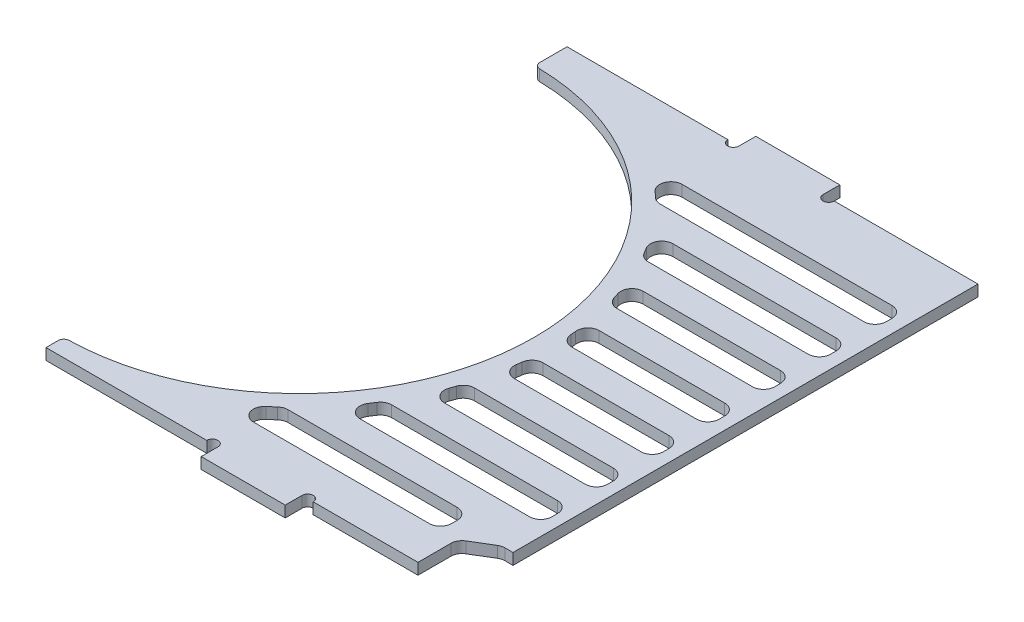
SolidWorks part; units mm, degrees
ref_plane "前视基准面" through (0, 0, 0) normal (0, 0, 1) x (1, 0, 0)
ref_plane "上视基准面" through (0, 0, 0) normal (0, 1, 0) x (1, 0, 0)
ref_plane "右视基准面" through (0, 0, 0) normal (1, 0, 0) x (0, 0, -1)
sketch "草图1" plane through (0, 0, 0) normal (0, 1, 0) x (1, 0, 0)
  line L0 (-38.2, -44.69) -> (-38.2, -45.85)
  line L1 (-38.2, 45.85) -> (38.2, 45.85)
  line L2 (-38.2, 45.85) -> (-38.2, 39.31)
  line L3 (-38.2, -45.85) -> (38.2, -45.85)
  line L4 (38.2, 45.85) -> (38.2, -45.85)
  line L5 (-38.2, 45.85) -> (38.2, -45.85) construction
  line L6 (-38.2, -45.85) -> (38.2, 45.85) construction
  arc A0 (-38.2, -44.69) -> (-38.2, 39.31) centre (-38.2, -2.69) ccw
  point P0 (0, 0)
  dimension "D4" = 84
  dimension "D1" = 91.7
  dimension "80" = 76.4
  dimension "D3" = 48.54
extrude "凸台-拉伸1" add sketch "草图1" along normal blind 2
sketch "草图3" plane through (0, 0, -45.85) normal (0, 0, -1) x (-1, 0, 0)
  line L4 (-38.2, 0) -> (38.2, 0)
  line L5 (38.2, 0) -> (38.2, 2)
  line L6 (38.2, 2) -> (-38.2, 2)
  line L7 (-38.2, 2) -> (-38.2, 0)
  line L8 (-38.2, 0) -> (38.2, 0)
  line L9 (38.2, 0) -> (38.2, 2)
  line L10 (38.2, 2) -> (-38.2, 2)
  line L11 (-38.2, 2) -> (-38.2, 0)
  dimension "D1" = 0
extrude "凸台-拉伸2" add sketch "草图3" along normal blind 7
sketch "草图5" plane through (0, 2, 0) normal (0, 1, 0) x (1, 0, 0)
  line L0 (-38.2, 51.26) -> (38.2, 52.85)
  line L1 (-38.2, 52.85) -> (-38.2, 39.31) construction
  line L2 (38.2, 52.85) -> (-38.2, 52.85)
  line L3 (-38.2, 52.85) -> (-38.2, 51.26)
  dimension "D1" = 1.59
extrude "切除-拉伸1" cut sketch "草图5" against normal blind 10
sketch "草图7" plane through (0, 0, 0) normal (0, -1, 0) x (1, 0, 0)
  line L0 (25.6, -52.5878) -> (25.6, -54.7548)
  line L1 (-38.2, -51.26) -> (38.2, -52.85) construction
  line L2 (25.6, -54.7548) -> (9.6, -54.7548)
  line L3 (9.6, -54.7548) -> (9.6, -52.2548)
  line L4 (9.6, -52.2548) -> (25.6, -52.5878)
  line L5 (38.2, 45.85) -> (38.2, -52.85) construction
  dimension "D1" = 16
  dimension "D2" = 2.5
  dimension "D3" = 12.6
extrude "凸台-拉伸4" add sketch "草图7" against normal blind 2
pattern_linear "阵列(线性)2" count 2 spacing 32 along (-0.9998, 0, 0.0208) of "凸台-拉伸4"
fillet "圆角3" radius 0.5 4 edges at (-22.3931, 1, -54.089) (-6.3931, 1, -54.089) (25.6, 1, -54.7548) (9.6, 1, -54.7548)
sketch "草图10" plane through (0, 2, 0) normal (0, 1, 0) x (1, 0, 0)
  line L2 (-38.8823, 53.9056) -> (39.5858, 55.5386)
  line L3 (39.5858, 55.5386) -> (39.5858, 48.5386)
  line L5 (39.5858, 48.5386) -> (-38.2, 46.9198)
  line L6 (-38.2, 51.26) -> (-38.2, 39.31) construction
  line L10 (-38.8823, 53.9056) -> (-39.2277, 52.8897)
  line L11 (-39.2277, 52.8897) -> (-38.2, 46.9198)
  line L12 (25.6, 52.5878) -> (38.2, 52.85) construction
  dimension "D1" = 7
  dimension "D2" = 180
extrude "切除-拉伸2" cut sketch "草图10" against normal blind 10
sketch "草图11" plane through (0, 2, 0) normal (0, 1, 0) x (1, 0, 0)
  line L0 (-38.2, 46.9198) -> (38.2, 49.5098)
  line L1 (38.2, 49.5098) -> (38.2, 48.5098)
  line L2 (38.2, 48.5098) -> (-38.2, 46.9198)
  dimension "D1" = 1
extrude "凸台-拉伸5" add sketch "草图11" against normal blind 2
sketch "草图13" plane through (0, 0, 0) normal (0, -1, 0) x (1, 0, 0)
  line L0 (38.2, -49.5098) -> (37.7, -49.4928)
  line L1 (38.2, -49.5098) -> (-38.2, -46.9198) construction
  line L2 (37.7, -49.4928) -> (38.2, 45.85)
  line L3 (38.2, 45.85) -> (38.2, -49.5098)
  dimension "D1" = 0.5
extrude "切除-拉伸3" cut sketch "草图13" against normal blind 10
sketch "草图16" plane through (0, 0, 0) normal (0, -1, 0) x (1, 0, 0)
  line L0 (-14.3502, 40.85) -> (33.1737, 40.85)
  line L1 (33.1737, 40.85) -> (32.728, -44.1488)
  line L2 (32.728, -44.1488) -> (-32.4386, -41.9397)
  line L6 (38.2, 45.85) -> (37.7, -49.4928) construction
  line L7 (37.7, -49.4928) -> (-38.2, -46.9198) construction
  line L8 (-38.2, 45.85) -> (38.2, 45.85) construction
  line L9 (37.7542, -39.1488) -> (-21.6316, -39.1488)
  line L10 (37.7542, -34.1488) -> (-21.6316, -34.1488)
  line L11 (37.7542, -29.1488) -> (-21.6316, -29.1488)
  line L12 (37.7542, -24.1488) -> (-21.6316, -24.1488)
  line L13 (37.7542, -19.1488) -> (-21.6316, -19.1488)
  line L14 (37.7542, -14.1488) -> (-21.6316, -14.1488)
  line L15 (37.7542, -9.1488) -> (-21.6316, -9.1488)
  line L16 (37.7542, -4.1488) -> (-21.6316, -4.1488)
  line L17 (37.7542, 0.8512) -> (-21.6316, 0.8512)
  line L18 (37.7542, 5.8512) -> (-21.6316, 5.8512)
  line L19 (37.7542, 10.8512) -> (-21.6316, 10.8512)
  line L20 (37.7542, 15.8512) -> (-21.6316, 15.8512)
  line L21 (37.7542, 20.8512) -> (-21.6316, 20.8512)
  line L22 (37.7542, 25.8512) -> (-21.6316, 25.8512)
  line L23 (37.7542, 30.8512) -> (-21.6316, 30.8512)
  line L24 (37.7542, 35.8512) -> (-21.6316, 35.8512)
  circle A0 centre (-38.2, 2.69) radius 45
  dimension "D3" = 90
  dimension "D1" = 5
  dimension "D2" = 85
  dimension "D4" = 5
  dimension "D5" = 5
  dimension "D6" = 5
extrude "切除-拉伸4" cut sketch "草图16" against normal blind 10 contours A0 L2 L1 L9 | A0 L10 L1 L11 | A0 L12 L1 L13 | A0 L14 L1 L15 | A0 L16 L1 L17 | A0 L18 L1 L19 | A0 L20 L1 L21 | A0 L22 L1 L23 | A0 L24 L1 L0
fillet "圆角5" radius 2 22 edges at (2.9725, 1, 20.8512) (0.3819, 1, 25.8512) (3.5307, 1, -14.1488) (33.0164, 1, 10.8512) (32.9115, 1, -9.1488) (32.9902, 1, 5.8512) (5.2148, 1, -9.1488) (4.8324, 1, 15.8512) (33.1737, 1, 40.85) (-6.3992, 1, -29.1488) (-14.3502, 1, 40.85) (32.8066, 1, -29.1488) (32.7804, 1, -34.1488) (-2.0797, 1, -24.1488) (32.9377, 1, -4.1488) (33.1213, 1, 30.8512) (6.6888, 1, 5.8512) (-3.1009, 1, 30.8512) (32.8853, 1, -14.1488) (-21.6316, 1, -39.1488) (32.7542, 1, -39.1488) (32.728, 1, -44.1488)
sketch "草图23" plane through (0, 0, 0) normal (0, -1, 0) x (1, 0, 0)
  line L3 (30.7437, -39.1488) -> (-21.2543, -39.1488)
  line L4 (32.7387, -42.0907) -> (32.7436, -41.1593)
  line L5 (-32.4386, -41.9397) -> (30.671, -44.0791)
  line L6 (30.7437, -39.1488) -> (-21.2543, -39.1488)
  line L7 (32.7387, -42.0907) -> (32.7436, -41.1593)
  line L8 (-32.4386, -41.9397) -> (30.671, -44.0791)
  arc A4 (-32.4386, -41.9397) -> (-21.9754, -39.2833) centre (-38.2, 2.69) ccw
  arc A5 (-21.2543, -39.1488) -> (-21.9754, -39.2833) centre (-21.2543, -41.1488) ccw
  arc A6 (32.7436, -41.1593) -> (30.7437, -39.1488) centre (30.7437, -41.1488) ccw
  arc A7 (30.671, -44.0791) -> (32.7387, -42.0907) centre (30.7388, -42.0802) ccw
  arc A8 (-32.4386, -41.9397) -> (-21.9754, -39.2833) centre (-38.2, 2.69) ccw
  arc A9 (-21.2543, -39.1488) -> (-21.9754, -39.2833) centre (-21.2543, -41.1488) ccw
  arc A10 (32.7436, -41.1593) -> (30.7437, -39.1488) centre (30.7437, -41.1488) ccw
  arc A11 (30.671, -44.0791) -> (32.7387, -42.0907) centre (30.7388, -42.0802) ccw
  dimension "D1" = 0
extrude "凸台-拉伸9" add sketch "草图23" against normal up to surface (2 mm away) up to face at (-5.8167, 2, 0.1112)
fillet "圆角6" radius 2 13 edges at (6.0538, 1, 10.8512) (33.0688, 1, 20.8512) (33.1475, 1, 35.8512) (33.0426, 1, 15.8512) (6.2773, 1, -4.1488) (-12.3562, 1, -34.1488) (1.1455, 1, -19.1488) (-7.7806, 1, 35.8512) (32.9639, 1, 0.8512) (32.8591, 1, -19.1488) (33.0951, 1, 25.8512) (32.8328, 1, -24.1488) (6.7624, 1, 0.8512)
fillet "圆角7" radius 1 3 edges at (-38.2, 1, -39.31) (-38.2, 1, -46.9198) (-38.2, 1, 44.69)
sketch "草图18" plane through (0, 0, 45.85) normal (0, 0, 1) x (1, 0, 0)
  line L4 (-38.2, 0) -> (38.2, 0)
  line L5 (38.2, 0) -> (38.2, 2)
  line L6 (38.2, 2) -> (-38.2, 2)
  line L7 (-38.2, 2) -> (-38.2, 0)
  line L8 (-38.2, 0) -> (38.2, 0)
  line L9 (38.2, 0) -> (38.2, 2)
  line L10 (38.2, 2) -> (-38.2, 2)
  line L11 (-38.2, 2) -> (-38.2, 0)
  dimension "D1" = 0
extrude "凸台-拉伸6" add sketch "草图18" along normal blind 2
sketch "草图19" plane through (0, 2, 0) normal (0, 1, 0) x (1, 0, 0)
  line L1 (38.2, -47.85) -> (28.2, -47.85)
  line L2 (38.2, -47.85) -> (38.2, -37.85)
  line L3 (38.2, -37.85) -> (28.2, -37.85)
  line L4 (28.2, -47.85) -> (28.2, -37.85)
  dimension "D1" = 10
  dimension "D2" = 10
extrude "切除-拉伸5" cut sketch "草图19" against normal through all
sketch "草图20" plane through (0, 2, 0) normal (0, 1, 0) x (1, 0, 0)
  line L1 (-7.012, -35.8512) -> (31.158, -35.8512) construction
  line L2 (25.2, -35.8512) -> (33.158, -35.8512)
  line L3 (33.158, -35.8512) -> (33.158, -37.85)
  line L4 (33.158, -37.85) -> (28.2, -40.85)
  line L5 (25.2, -35.8512) -> (25.2, -40.85)
  line L6 (28.2, -40.85) -> (-8.1758, -40.85) construction
  line L7 (25.2, -40.85) -> (28.2, -40.85)
  dimension "D1" = 1.9988
  dimension "D2" = 3
extrude "凸台-拉伸8" add sketch "草图20" against normal up to surface (2 mm away) up to face at (12.4447, 0, -31.327)
fillet "圆角8" radius 2 2 edges at (25.2, 1, 35.8512) (25.2, 1, 40.85)
fillet "圆角9" radius 2 2 edges at (28.2, 1, 40.85) (33.158, 1, 37.85)
sketch "草图21" plane through (0, 0, 0) normal (0, -1, 0) x (1, 0, 0)
  line L1 (38.158, 37.85) -> (35.158, 37.85)
  line L2 (38.158, 37.85) -> (38.158, -49.4928)
  line L3 (38.158, -49.4928) -> (35.158, -49.4928)
  line L4 (35.158, 37.85) -> (35.158, -49.4928)
  dimension "D1" = 3
  dimension "D2" = 87.3428
extrude "切除-拉伸6" cut sketch "草图21" against normal through all
sketch "草图22" plane through (0, 0, 0) normal (0, -1, 0) x (1, 0, 0)
  line L0 (-39.2441, -47.15) -> (-39.2441, -45.15) construction
  line L1 (-39.2441, -47.15) -> (-31.4091, -47.15) construction
  line L2 (35.158, -49.4067) -> (-37.2339, -46.9525) construction
  line L3 (-39.2441, -45.15) -> (60.7559, -45.15)
  line L4 (60.7559, -45.15) -> (60.7559, -51.15)
  line L5 (60.7559, -51.15) -> (-39.2441, -51.15)
  line L6 (-39.2441, -51.15) -> (-39.2441, -47.15)
  dimension "D1" = 2
  dimension "D2" = 6
  dimension "D3" = 100
extrude "切除-拉伸7" cut sketch "草图22" against normal through all and the other way through all flip side to cut
sketch "草图24" plane through (0, 0, -45.15) normal (0, 0, -1) x (-1, 0, 0)
  line L0 (38.2, 2) -> (-35.158, 2) construction
  line L1 (-7.5, 2) -> (7.5, 2)
  line L2 (-7.5, 2) -> (-7.5, 0)
  line L3 (-7.5, 0) -> (7.5, 0)
  line L4 (7.5, 2) -> (7.5, 0)
  point P7 (0, 2)
  dimension "D1" = 15
  dimension "D2" = 2
extrude "凸台-拉伸10" add sketch "草图24" along normal blind 3
sketch "草图25" plane through (0, 2, 0) normal (0, 1, 0) x (1, 0, 0)
  line L0 (-38.2, 45.15) -> (-7.5, 45.15) construction
  line L1 (7.5, 45.15) -> (35.158, 45.15) construction
  circle A0 centre (-8.5, 45.15) radius 1
  circle A1 centre (8.5, 45.15) radius 1
  dimension "D1" = 2
extrude "切除-拉伸8" cut sketch "草图25" against normal through all
ref_plane "基准面1" through (0, 0, 1.35) normal (0, 0, 1) x (1, 0, 0)
mirror "镜向1" about plane through (0, 0, 1.35) normal (0, 0, 1) of "切除-拉伸8", "凸台-拉伸10"
